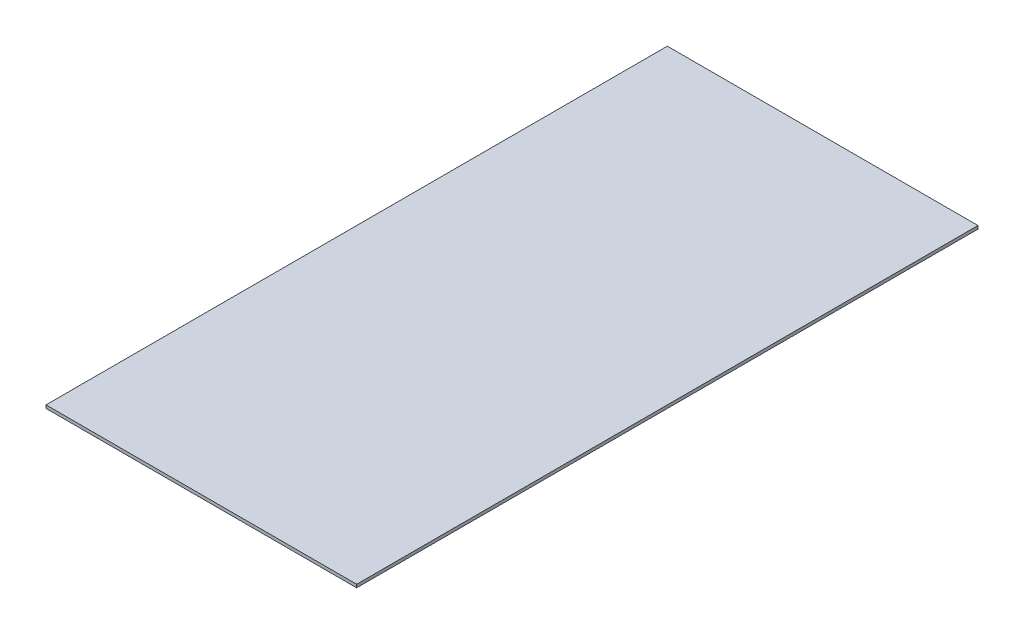
SolidWorks part; units mm, degrees
ref_plane "Front Plane" through (0, 0, 0) normal (0, 0, 1) x (1, 0, 0)
ref_plane "Top Plane" through (0, 0, 0) normal (0, 1, 0) x (1, 0, 0)
ref_plane "Right Plane" through (0, 0, 0) normal (1, 0, 0) x (0, 0, -1)
sketch "Sketch1" plane through (0, 0, 0) normal (0, 1, 0) x (1, 0, 0)
  line L1 (500, -1000) -> (-500, -1000)
  line L2 (500, -1000) -> (500, 1000)
  line L3 (500, 1000) -> (-500, 1000)
  line L4 (-500, -1000) -> (-500, 1000)
  line L5 (500, -1000) -> (-500, 1000) construction
  line L6 (500, 1000) -> (-500, -1000) construction
  point P0 (0, 0)
  dimension "D1" = 1000
  dimension "D2" = 2000
extrude "Boss-Extrude1" add sketch "Sketch1" against normal mid plane 10
